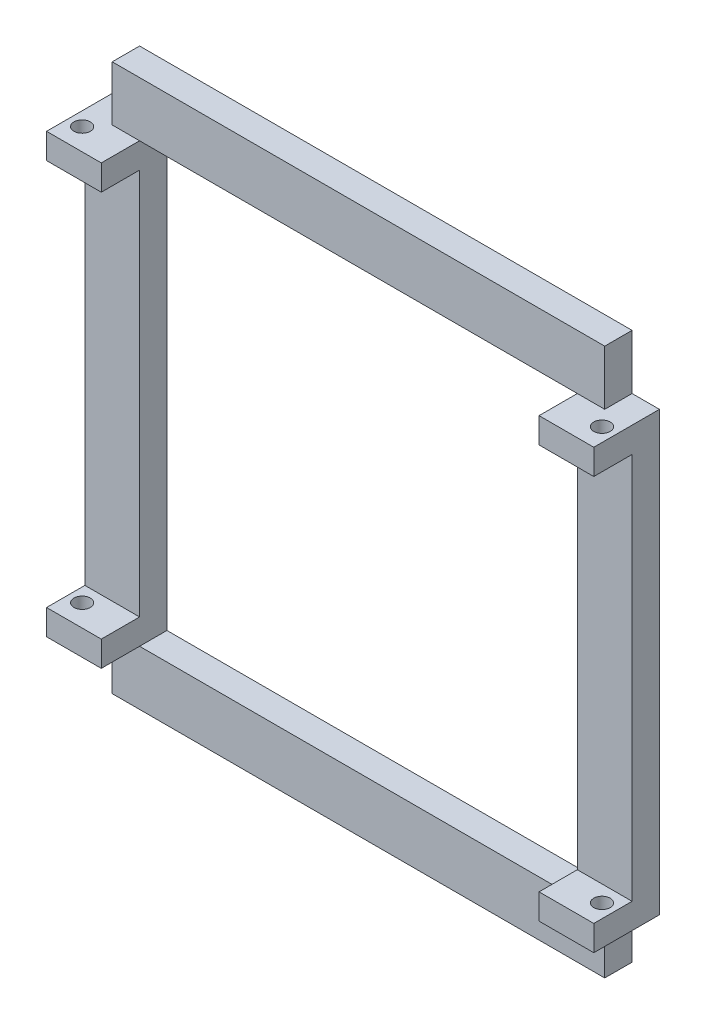
SolidWorks part; units mm, degrees
ref_plane "Front Plane" through (0, 0, 0) normal (0, 0, 1) x (1, 0, 0)
ref_plane "Top Plane" through (0, 0, 0) normal (0, 1, 0) x (1, 0, 0)
ref_plane "Right Plane" through (0, 0, 0) normal (1, 0, 0) x (0, 0, -1)
sketch "Sketch1" plane through (0, 0, 0) normal (0, 0, 1) x (1, 0, 0)
  line L0 (-50, 40) -> (-45, 40)
  line L1 (45, 50) -> (-45, 50)
  line L2 (50, 40) -> (50, -40)
  line L3 (45, -50) -> (-45, -50)
  line L4 (-50, 40) -> (-50, -40)
  line L5 (45, 36.5791) -> (-45, -36.5791) construction
  line L6 (45, -36.5791) -> (-45, 36.5791) construction
  line L7 (-45, 40) -> (-45, 50)
  line L8 (0, -57.4776) -> (0, 57.4776) construction
  line L9 (50, 40) -> (45, 40)
  line L10 (45, 40) -> (45, 50)
  line L11 (60.0657, 0) -> (-60.0657, 0) construction
  line L12 (-45, -40) -> (-45, -50)
  line L13 (-50, -40) -> (-45, -40)
  line L14 (50, -40) -> (45, -40)
  line L15 (45, -40) -> (45, -50)
  line L17 (-40, 40) -> (40, 40)
  line L18 (-40, 40) -> (-40, -40)
  line L19 (-40, -40) -> (40, -40)
  line L20 (40, 40) -> (40, -40)
  line L21 (-40, 40) -> (40, -40) construction
  line L22 (-40, -40) -> (40, 40) construction
  point P0 (0, 0)
  point P4 (0, 0)
  dimension "D1" = 10
  dimension "D2" = 5
  dimension "D3" = 100
  dimension "D4" = 100
  dimension "D5" = 80
  dimension "D6" = 80
extrude "Boss-Extrude1" add sketch "Sketch1" along normal blind 5
sketch "Sketch2" plane through (0, 0, 5) normal (0, 0, 1) x (1, 0, 0)
  line L0 (40, -40) -> (40, 40) construction
  line L1 (50, -40) -> (40, -40)
  line L2 (50, -40) -> (50, -35.3624)
  line L3 (50, -35.3624) -> (40, -35.3624)
  line L4 (40, -40) -> (40, -35.3624)
  line L5 (0, -2.75) -> (0, 2.75) construction
  line L6 (-50, -35.3624) -> (-40, -35.3624)
  line L7 (-40, -40) -> (-40, -35.3624)
  line L8 (-50, -40) -> (-40, -40)
  line L9 (-50, -40) -> (-50, -35.3624)
  line L10 (2.75, 0) -> (-2.75, 0) construction
  line L11 (-50, 40) -> (-50, 35.3624)
  line L12 (-50, 40) -> (-40, 40)
  line L13 (-40, 40) -> (-40, 35.3624)
  line L14 (-50, 35.3624) -> (-40, 35.3624)
  line L15 (40, 40) -> (40, 35.3624)
  line L16 (50, 35.3624) -> (40, 35.3624)
  line L17 (50, 40) -> (50, 35.3624)
  line L18 (50, 40) -> (40, 40)
extrude "Boss-Extrude2" add sketch "Sketch2" along normal blind 7
sketch "Sketch3" plane through (0, -40, 0) normal (0, -1, 0) x (1, 0, 0)
  line L2 (-47.5, 8) -> (-50, 8) construction
  line L3 (-50, 12) -> (-50, 0) construction
  line L4 (-50, 0) -> (-45, 0) construction
  line L5 (0, -6.6) -> (0, 6.6) construction
  circle A0 centre (-47.5, 8) radius 1.5
  circle A1 centre (47.5, 8) radius 1.5
  dimension "D1" = 3
  dimension "D2" = 2.5
  dimension "D3" = 8
extrude "Cut-Extrude1" cut sketch "Sketch3" against normal through all
